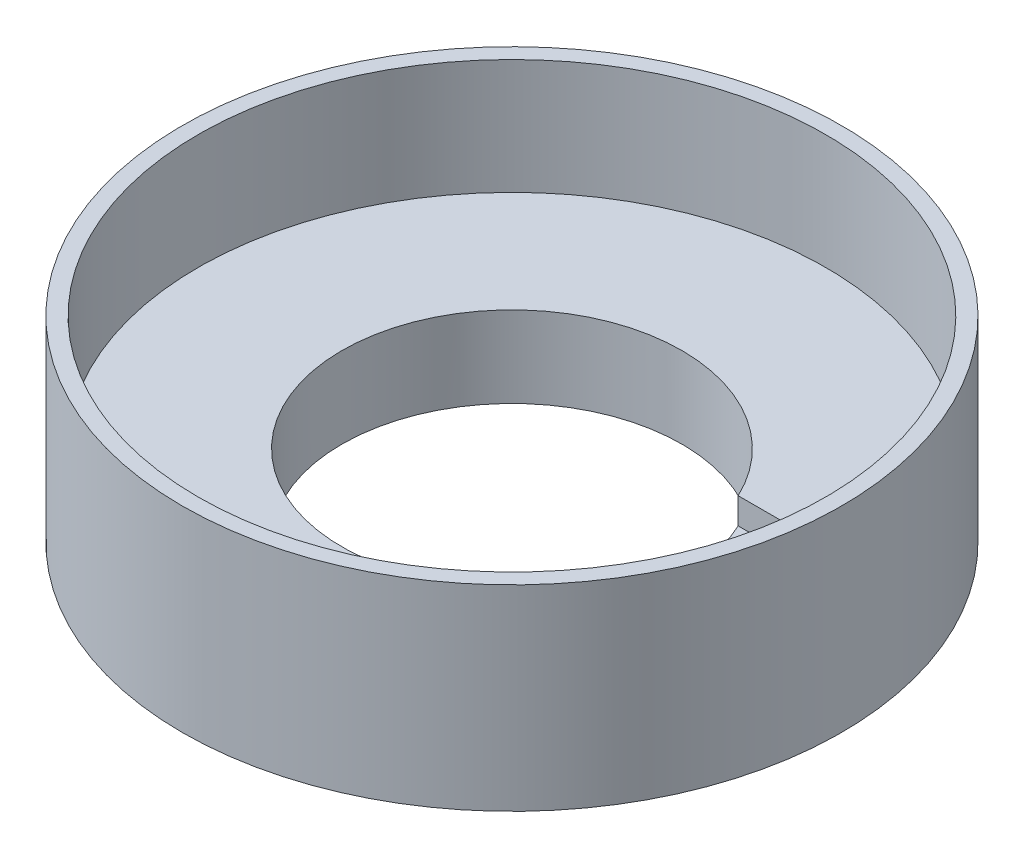
SolidWorks part; units mm, degrees
ref_plane "Front Plane" through (0, 0, 0) normal (0, 0, 1) x (1, 0, 0)
ref_plane "Top Plane" through (0, 0, 0) normal (0, 1, 0) x (1, 0, 0)
ref_plane "Right Plane" through (0, 0, 0) normal (1, 0, 0) x (0, 0, -1)
sketch "Sketch4" plane through (0, 0, 0) normal (0, 1, 0) x (1, 0, 0)
  circle A0 centre (0, 0) radius 32.5
  circle A1 centre (0, 0) radius 63
  dimension "D1" = 126
  dimension "D2" = 65
extrude "Boss-Extrude1" add sketch "Sketch4" along normal blind 15.5
sketch "Sketch5" plane through (0, 15.5, 0) normal (0, 1, 0) x (1, 0, 0)
  circle A0 centre (0, 0) radius 60
  circle A1 centre (0, 0) radius 63
  dimension "D1" = 120
  dimension "D2" = 126
extrude "Boss-Extrude2" add sketch "Sketch5" along normal blind 22
sketch "Sketch7" plane through (0, 15.5, 0) normal (0, 1, 0) x (1, 0, 0)
  line L1 (19.9548, -10.411) -> (44.9548, -10.411)
  line L2 (19.9548, -10.411) -> (19.9548, 13.8367)
  line L3 (19.9548, 13.8367) -> (44.9548, 13.8367)
  line L4 (44.9548, -10.411) -> (44.9548, 13.8367)
  line L5 (19.9548, -10.411) -> (44.9548, 13.8367) construction
  line L6 (19.9548, 13.8367) -> (44.9548, -10.411) construction
  circle A0 centre (0, 0) radius 32.5 construction
  point P0 (32.4548, 1.7129)
  dimension "D1" = 25
extrude "Cut-Extrude1" cut sketch "Sketch7" against normal blind 5
